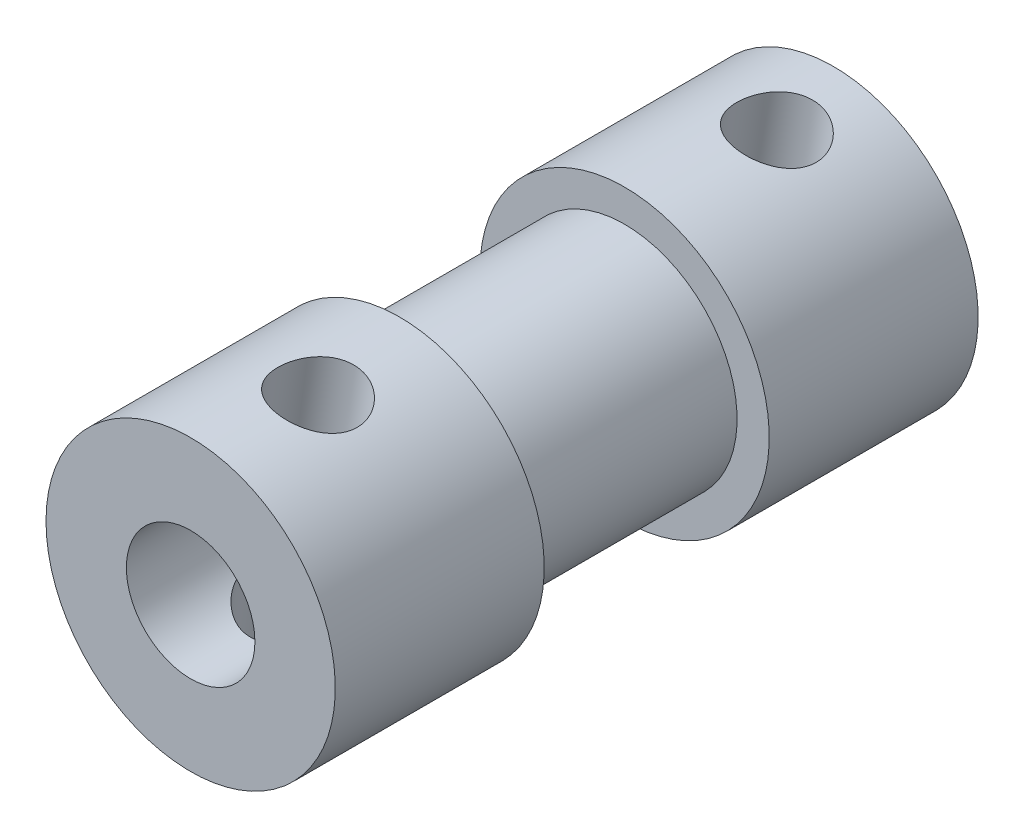
SolidWorks part; units mm, degrees
ref_plane "Front Plane" through (0, 0, 0) normal (0, 0, 1) x (1, 0, 0)
ref_plane "Top Plane" through (0, 0, 0) normal (0, 1, 0) x (1, 0, 0)
ref_plane "Right Plane" through (0, 0, 0) normal (1, 0, 0) x (0, 0, -1)
sketch "Sketch1" plane through (0, 0, 0) normal (0, 1, 0) x (1, 0, 0)
  line L0 (0, 0) -> (3.5, 0) construction
  line L1 (4.5, 10) -> (0, 10)
  line L2 (3.5, -3.5) -> (3.5, 3.5)
  line L3 (3.5, 3.5) -> (4.5, 3.5)
  line L4 (4.5, 3.5) -> (4.5, 10)
  line L5 (0, 10) -> (0, -10)
  line L6 (4.5, -3.5) -> (4.5, -10)
  line L7 (3.5, -3.5) -> (4.5, -3.5)
  line L8 (4.5, -10) -> (0, -10)
  dimension "D1" = 20
  dimension "D2" = 4.5
  dimension "D3" = 3.5
  dimension "D4" = 6.5
revolve "Revolve1" add sketch "Sketch1" angle 360 about L5
hole_wizard "Ø4.0mm Dowel Hole1" positions "Sketch2" profile "Sketch3" hole size "Ø4.0" standard "ANSI Metric" end condition through all
sketch "Sketch2" plane through (0, 0, 10) normal (0, 0, 1) x (1, 0, 0)
  point P0 (0, 0)
sketch "Sketch3" plane through (0, 0, 10) normal (1, 0, 0) x (0, -1, 0)
  line L0 (0, 0) -> (0, 20)
  line L1 (0, 20) -> (2, 20)
  line L2 (2, 20) -> (2, 0)
  line L5 (2, 0) -> (0, 0)
  line L11 (0, -6.35) -> (0, 107.95) construction
  dimension "Thru Hole Dia." = 4
  dimension "Thru Hole Depth" = 20
hole_wizard "M3x0.5 Tapped Hole1" positions "3DSketch1" profile "Sketch4" tap size "M3x0.5" standard "ANSI Metric"
sketch3d "3DSketch1"
  line L5 (0, 0, 10) -> (0, 4.5, 10) construction
  line L6 (0, 0, 10) -> (0, 0, 3.5) construction
  line L7 (0, 4.5, 10) -> (0, 4.5, 3.5) construction
  line L9 (0, 4.5, 3.5) -> (0, 4.5, -3.5) construction
  line L10 (0, 4.5, -3.5) -> (0, 4.5, -10) construction
  circle A0 centre (0, 0, 10) radius 4.5 construction
  circle A1 centre (0, 0, 3.5) radius 4.5 construction
  circle A2 centre (0, 0, -3.5) radius 4.5 construction
  circle A3 centre (0, 0, -10) radius 4.5 construction
  point P28 (0, 0, 5.5)
  point P32 (0, 0, -1)
  point P38 (0, 0, -8)
  point P42 (0, 0, -14.5)
  point P44 (0, 4.5, 6.75)
  point P46 (0, 4.5, -6.75)
  point P51 (0.6888, 4.447, -7.5624)
  point P65 (0, 4.5, 6.75)
  point P68 (0.6888, 4.447, 6.7128)
cosmetic thread "Hole Thread3" parameters "D2"=3
cosmetic thread "Hole Thread4" parameters "D2"=3
sketch "Sketch4" plane through (0.6888, 4.447, 6.7128) normal (0, 0, 1) x (-0.9882, 0.1531, 0)
  line L0 (0, 0) -> (0, 9.6358)
  line L1 (0, 9.6358) -> (1.25, 9.6358)
  line L2 (1.25, 9.6358) -> (1.25, 0)
  line L5 (1.25, 0) -> (0, 0)
  line L11 (0, -6.35) -> (0, 107.95) construction
  dimension "Thru Tap Drill Dia." = 2.5
  dimension "Thru Tap Drill Depth" = 9.6358
